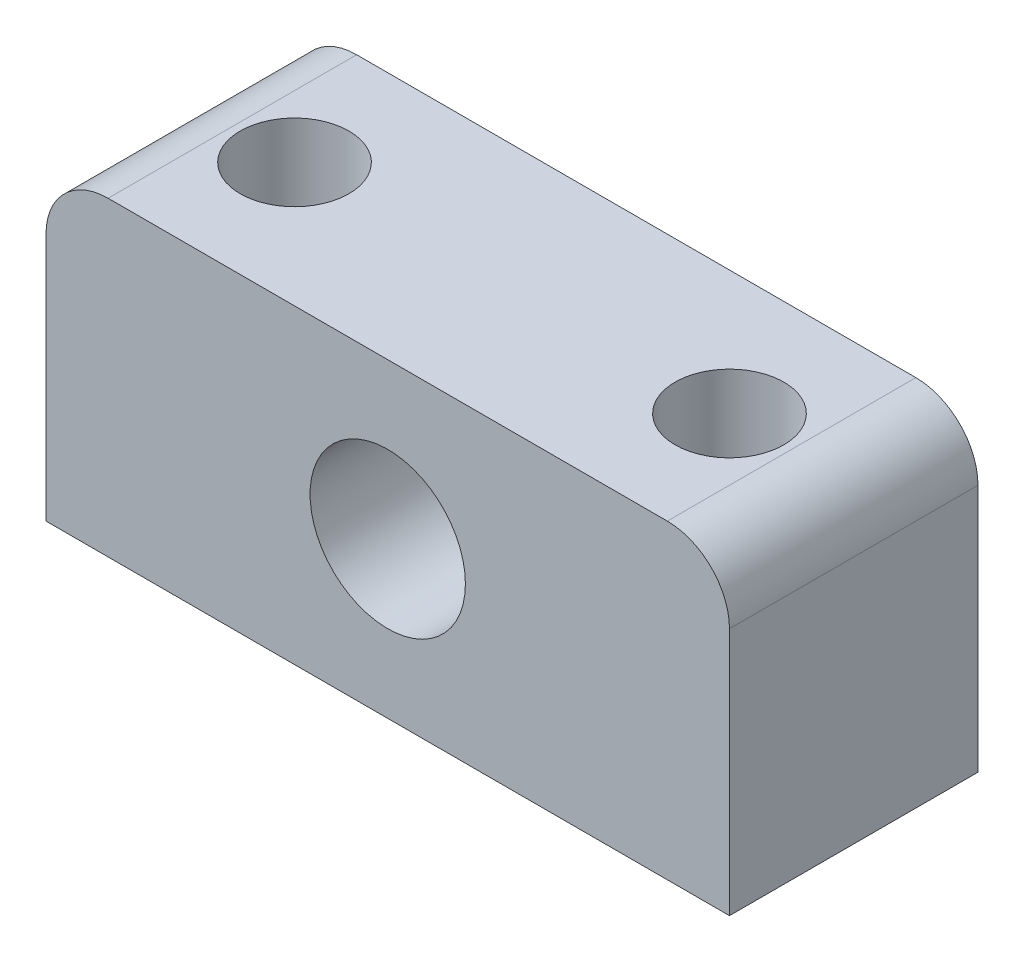
SolidWorks part; units mm, degrees
ref_plane "正面(Front)" through (0, 0, 0) normal (0, 0, 1) x (1, 0, 0)
ref_plane "平面(Top)" through (0, 0, 0) normal (0, 1, 0) x (1, 0, 0)
ref_plane "右側面(Right)" through (0, 0, 0) normal (1, 0, 0) x (0, 0, -1)
sketch "ｽｹｯﾁ1" plane through (0, 0, 0) normal (0, 0, 1) x (1, 0, 0)
  line L1 (-11, 5) -> (11, 5)
  line L2 (-11, 5) -> (-11, -5)
  line L3 (-11, -5) -> (11, -5)
  line L4 (11, 5) -> (11, -5)
  line L5 (-11, 5) -> (11, -5) construction
  line L6 (-11, -5) -> (11, 5) construction
  circle A0 centre (0, 0) radius 2.5
  point P0 (0, 0)
  dimension "D3" = 5
  dimension "D1" = 22
  dimension "D2" = 10
extrude "ﾎﾞｽ - 押し出し1" add sketch "ｽｹｯﾁ1" along normal mid plane 8
sketch "ｽｹｯﾁ3" plane through (0, 5, 0) normal (0, 1, 0) x (1, 0, 0)
  line L0 (0, 0) -> (0, 8.9645) construction
  circle A0 centre (7, 0) radius 1.75
  circle A1 centre (-7, 0) radius 1.75
  point P5 (7.3384, 0)
  dimension "D1" = 3.5
  dimension "D2" = 7
extrude "ｶｯﾄ - 押し出し1" cut sketch "ｽｹｯﾁ3" against normal through all
fillet "ﾌｨﾚｯﾄ1" radius 2 2 edges at (11, 5, 0) (-11, 5, 0)
